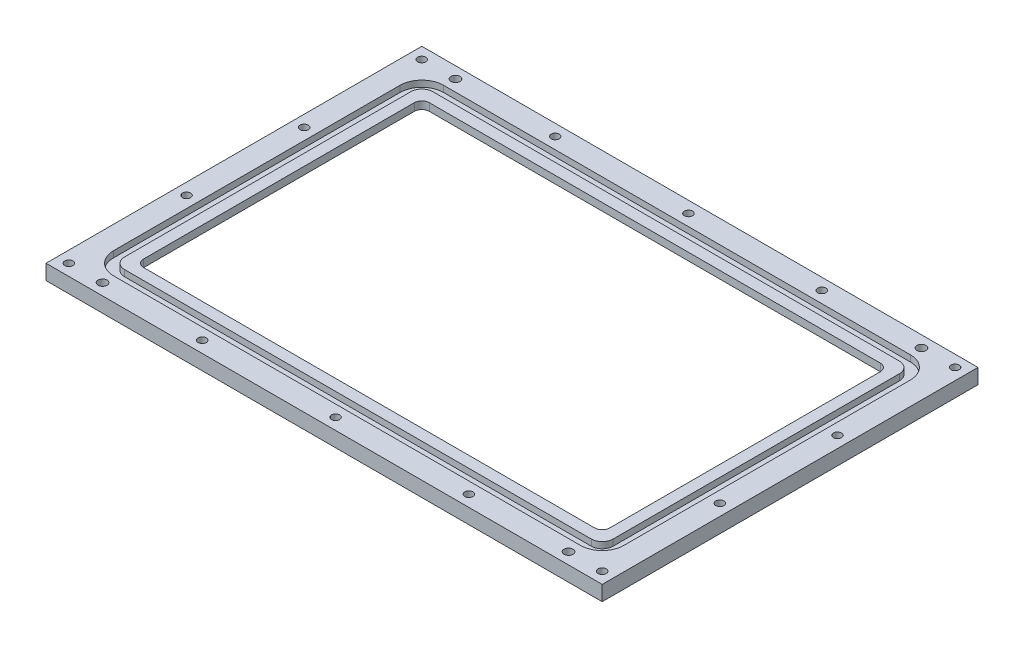
SolidWorks part; units mm, degrees
material "6061-T6 (SS)"
ref_plane "Front Plane" through (0, 0, 0) normal (0, 0, 1) x (1, 0, 0)
ref_plane "Top Plane" through (0, 0, 0) normal (0, 1, 0) x (1, 0, 0)
ref_plane "Right Plane" through (0, 0, 0) normal (1, 0, 0) x (0, 0, -1)
sketch "Sketch1" plane through (0, 0, 0) normal (0, 1, 0) x (1, 0, 0)
  line L1 (101.6, -63.5) -> (-101.6, -63.5)
  line L2 (101.6, -63.5) -> (101.6, 63.5)
  line L3 (101.6, 63.5) -> (-101.6, 63.5)
  line L4 (-101.6, -63.5) -> (-101.6, 63.5)
  line L5 (101.6, -63.5) -> (-101.6, 63.5) construction
  line L6 (101.6, 63.5) -> (-101.6, -63.5) construction
  point P0 (0, 0)
  dimension "D1" = 127
  dimension "D2" = 203.2
extrude "Boss-Extrude1" add sketch "Sketch1" along normal blind 6.35
sketch "Sketch2" plane through (0, 6.35, 0) normal (0, 1, 0) x (1, 0, 0)
  line L8 (-98.425, 60.325) -> (-98.425, -60.325)
  line L9 (98.425, 60.325) -> (-98.425, 60.325)
  line L10 (98.425, -60.325) -> (98.425, 60.325)
  line L11 (-98.425, -60.325) -> (98.425, -60.325)
  line L12 (-98.425, 60.325) -> (-98.425, -60.325)
  line L13 (98.425, 60.325) -> (-98.425, 60.325)
  line L14 (98.425, -60.325) -> (98.425, 60.325)
  line L15 (-98.425, -60.325) -> (98.425, -60.325)
  dimension "D1" = 3.175
extrude "Cut-Extrude1" cut sketch "Sketch2" against normal through all
sketch "Sketch4" plane through (0, 6.35, 0) normal (0, 1, 0) x (1, 0, 0)
  line L0 (-101.6, 63.5) -> (-101.6, -63.5)
  line L1 (-101.6, -63.5) -> (101.6, -63.5)
  line L2 (101.6, -63.5) -> (101.6, 63.5)
  line L3 (101.6, 63.5) -> (-101.6, 63.5)
  line L4 (117.475, 79.375) -> (-117.475, 79.375)
  line L5 (-117.475, 79.375) -> (-117.475, -79.375)
  line L6 (-117.475, -79.375) -> (117.475, -79.375)
  line L7 (117.475, -79.375) -> (117.475, 79.375)
  dimension "D1" = 15.875
extrude "Boss-Extrude2" add sketch "Sketch4" against normal blind 6.35
sketch "Sketch7" plane through (0, 6.35, 0) normal (0, 1, 0) x (1, 0, 0)
  line L1 (-98.425, -60.325) -> (98.425, -60.325) construction
  line L2 (-98.425, 60.325) -> (-98.425, -60.325) construction
  line L3 (98.425, 60.325) -> (-98.425, 60.325) construction
  line L4 (-107.8103, 69.7103) -> (-107.8103, -69.7103)
  line L5 (-107.8103, -69.7103) -> (107.8103, -69.7103)
  line L6 (107.8103, -69.7103) -> (107.8103, 69.7103)
  line L7 (107.8103, 69.7103) -> (-107.8103, 69.7103)
  line L8 (98.425, -60.325) -> (98.425, 60.325) construction
  line L12 (-103.1875, -65.0875) -> (103.1875, -65.0875)
  line L13 (103.1875, -65.0875) -> (103.1875, 65.0875)
  line L14 (103.1875, 65.0875) -> (-103.1875, 65.0875)
  line L15 (-103.1875, 65.0875) -> (-103.1875, -65.0875)
  dimension "D1" = 4.7625
  dimension "D3" = 4.7625
  dimension "D4" = 4.7625
  dimension "D5" = 4.7625
  dimension "D2" = 4.6228
extrude "Cut-Extrude2" cut sketch "Sketch7" against normal blind 2.6416
hole_wizard "#8-32 Tapped Hole1" positions "Sketch6" profile "Sketch5" tap size "#8-32" standard "ANSI Inch" end condition through all
sketch "Sketch6" plane through (0, 6.35, 0) normal (0, 1, 0) x (1, 0, 0)
  line L0 (0, 0) -> (0, 79.375) construction
  line L1 (117.475, 79.375) -> (-117.475, 79.375) construction
  line L4 (0, 0) -> (117.475, 0) construction
  line L5 (117.475, -79.375) -> (117.475, 79.375) construction
  line L6 (0, 74.5427) -> (56.3213, 74.5427) construction
  line L7 (56.3213, 74.5427) -> (112.6427, 74.5427) construction
  line L10 (112.6427, 74.5427) -> (112.6427, 24.8476) construction
  line L13 (112.6427, 24.8476) -> (112.6427, -24.8476) construction
  line L16 (107.8103, 69.7103) -> (117.475, 79.375) construction
  point P22 (56.3213, 74.5427)
  point P24 (112.6427, 74.5427)
  point P26 (112.6427, 24.8476)
  point P110 (0, 74.5427)
  point P132 (112.6427, -24.8476)
  point P133 (112.6427, -74.5427)
  point P134 (56.3213, -74.5427)
  point P135 (0, -74.5427)
  point P145 (-56.3213, -74.5427)
  point P146 (-112.6427, -74.5427)
  point P147 (-112.6427, -24.8476)
  point P148 (-112.6427, 24.8476)
  point P149 (-112.6427, 74.5427)
  point P150 (-56.3213, 74.5427)
sketch "Sketch5" plane through (56.3213, 6.35, -74.5427) normal (1, 0, 0) x (0, 0, 1)
  line L0 (0, 0) -> (0, 6.35)
  line L1 (0, 6.35) -> (1.7272, 6.35)
  line L2 (1.7272, 6.35) -> (1.7272, 0)
  line L5 (1.7272, 0) -> (0, 0)
  line L11 (0, -6.35) -> (0, 107.95) construction
  dimension "Thread Major Dia." = 3.4544
  dimension "Thru Tap Drill Depth" = 6.35
sketch "O Ring Corner Fillet Dimentions" plane through (0, 6.35, 0) normal (0, 1, 0) x (1, 0, 0)
  line L0 (107.8103, 69.7103) -> (98.5647, 60.4647) construction
  line L1 (107.8103, 69.7103) -> (-107.8103, 69.7103) construction
  line L2 (107.8103, -69.7103) -> (107.8103, 69.7103) construction
  circle A0 centre (98.5647, 60.4647) radius 9.2456
  circle A1 centre (98.5647, 60.4647) radius 4.6228
  dimension "D1" = 4.6228
  dimension "D2" = 18.4912
  dimension "D3" = 9.2456
fillet "Fillet3" radius 4.6228 4 edges at (103.1875, 5.0292, 65.0875) (-103.1875, 5.0292, 65.0875) (-103.1875, 5.0292, -65.0875) (103.1875, 5.0292, -65.0875)
fillet "Fillet4" radius 9.2456 4 edges at (107.8103, 5.0292, 69.7103) (-107.8103, 5.0292, 69.7103) (-107.8103, 5.0292, -69.7103) (107.8103, 5.0292, -69.7103)
fillet "Fillet5" radius 3.175 4 edges at (98.425, 3.175, -60.325) (-98.425, 3.175, 60.325) (98.425, 3.175, 60.325) (-98.425, 3.175, -60.325)
hole_wizard "#6 Clearance Hole1" positions "Sketch15" profile "Sketch14" hole size "#6" standard "ANSI Inch" end condition through all
sketch "Sketch15" plane through (0, 0, 0) normal (0, -1, 0) x (-1, 0, 0)
  line L1 (0, 0) -> (0, 87.6055) construction
  line L4 (0, 0) -> (66.1414, 0) construction
  line L7 (-112.6427, 74.5427) -> (-56.3213, 74.5427) construction
  point P2 (-98.425, 74.5427)
  point P31 (-98.425, -74.5427)
  point P32 (98.425, -74.5427)
  point P33 (98.425, 74.5427)
  point P34 (-98.425, 74.5427)
  point P36 (98.425, 74.5427)
  point P38 (98.425, -74.5427)
  point P40 (-98.425, -74.5427)
sketch "Sketch14" plane through (98.425, 0, -74.5427) normal (1, 0, 0) x (0, 0, -1)
  line L0 (0, 0) -> (0, 6.35)
  line L1 (0, 6.35) -> (1.8986, 6.35)
  line L2 (1.8986, 6.35) -> (1.8986, 0)
  line L5 (1.8986, 0) -> (0, 0)
  line L11 (0, -6.35) -> (0, 107.95) construction
  dimension "Thru Hole Dia." = 3.7973
  dimension "Thru Hole Depth" = 6.35
sketch "Sketch18" plane through (0, 0, 0) normal (0, -1, 0) x (1, 0, 0)
  line L0 (95.25, -60.325) -> (-95.25, -60.325) construction
  line L1 (101.6, 63.5) -> (-101.6, 63.5)
  line L2 (101.6, 63.5) -> (101.6, -63.5)
  line L3 (101.6, -63.5) -> (-101.6, -63.5)
  line L4 (-101.6, 63.5) -> (-101.6, -63.5)
  line L5 (101.6, 63.5) -> (-101.6, -63.5) construction
  line L6 (101.6, -63.5) -> (-101.6, 63.5) construction
  line L7 (98.425, 57.15) -> (98.425, -57.15) construction
  point P0 (0, 0)
  dimension "D1" = 3.175
  dimension "D2" = 3.175
extrude "Cut-Extrude3" cut sketch "Sketch18" against normal blind 3.175
fillet "Fillet6" radius 3.175 4 edges at (-101.6, 1.5875, 63.5) (101.6, 1.5875, 63.5) (-101.6, 1.5875, -63.5) (101.6, 1.5875, -63.5)
